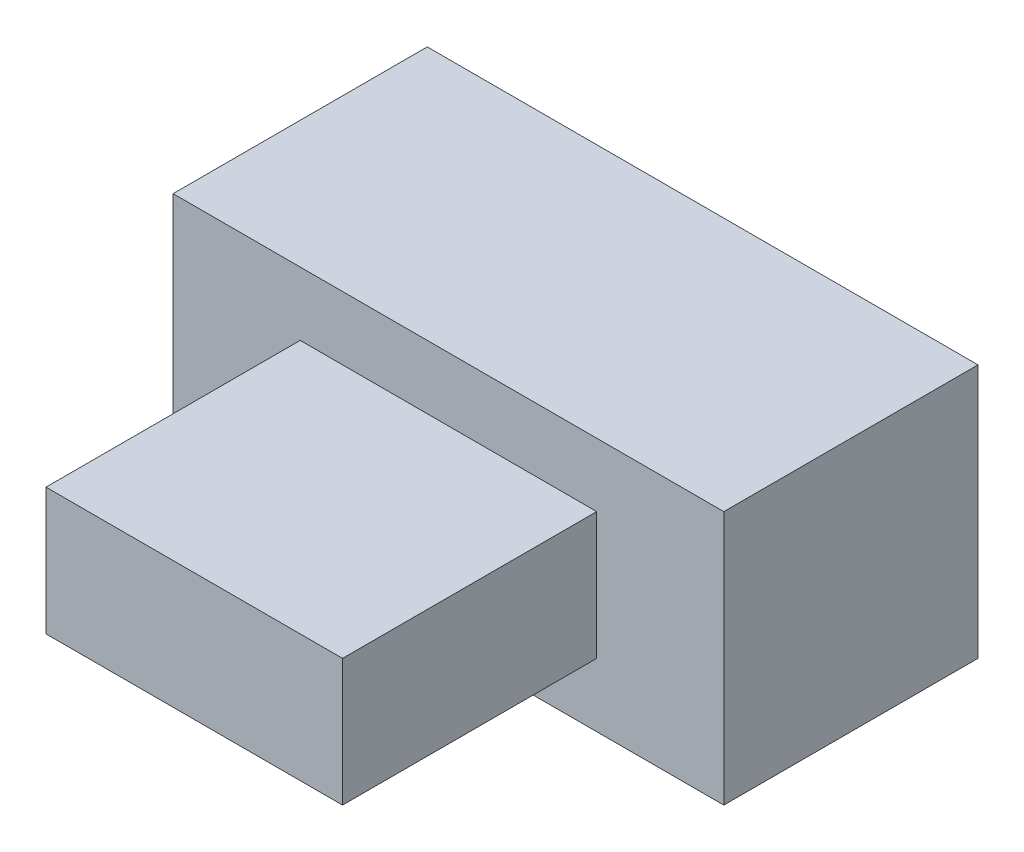
SolidWorks part; units mm, degrees
ref_plane "Front Plane" through (0, 0, 0) normal (0, 0, 1) x (1, 0, 0)
ref_plane "Top Plane" through (0, 0, 0) normal (0, 1, 0) x (1, 0, 0)
ref_plane "Right Plane" through (0, 0, 0) normal (1, 0, 0) x (0, 0, -1)
sketch "Sketch1" plane through (0, 0, 0) normal (0, 0, 1) x (1, 0, 0)
  line L1 (0, 0) -> (13, 0)
  line L2 (0, 0) -> (0, 6)
  line L3 (0, 6) -> (13, 6)
  line L4 (13, 0) -> (13, 6)
  dimension "D1" = 6
  dimension "D2" = 13
extrude "Boss-Extrude1" add sketch "Sketch1" along normal blind 6
sketch "Sketch2" plane through (0, 0, 6) normal (0, 0, 1) x (1, 0, 0)
  line L0 (13, 6) -> (0, 6) construction
  line L1 (3, 4.5) -> (10, 4.5)
  line L2 (3, 4.5) -> (3, 1.5)
  line L3 (3, 1.5) -> (10, 1.5)
  line L4 (10, 4.5) -> (10, 1.5)
  line L5 (13, 0) -> (13, 6) construction
  point P4 (6.5, 4.5)
  point P7 (6.5, 6)
  point P8 (10, 3)
  point P11 (13, 3)
  dimension "D1" = 3
  dimension "D2" = 7
extrude "Boss-Extrude2" add sketch "Sketch2" along normal blind 6
